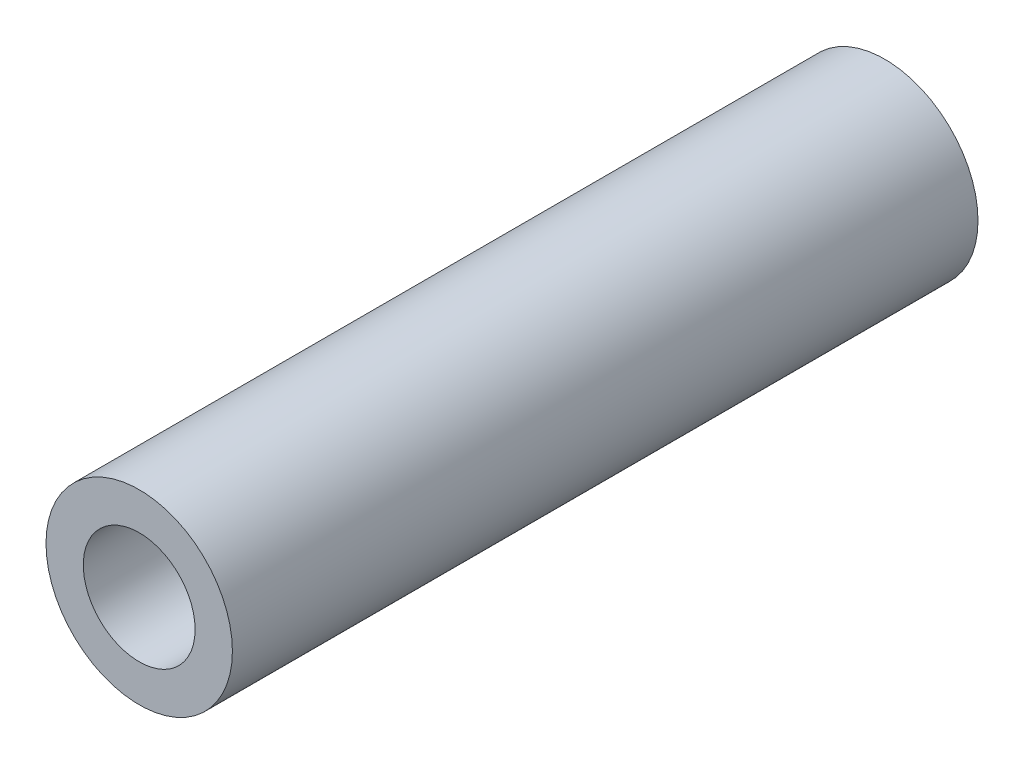
SolidWorks part; units mm, degrees
ref_plane "前视基准面" through (0, 0, 0) normal (0, 0, 1) x (1, 0, 0)
ref_plane "上视基准面" through (0, 0, 0) normal (0, 1, 0) x (1, 0, 0)
ref_plane "右视基准面" through (0, 0, 0) normal (1, 0, 0) x (0, 0, -1)
sketch "草图1" plane through (0, 0, 0) normal (0, 0, 1) x (1, 0, 0)
  circle A0 centre (0, 0) radius 2.5
  circle A1 centre (0, 0) radius 1.5
  dimension "D1" = 3
  dimension "D2" = 5
extrude "凸台-拉伸1" add sketch "草图1" along normal mid plane 20
